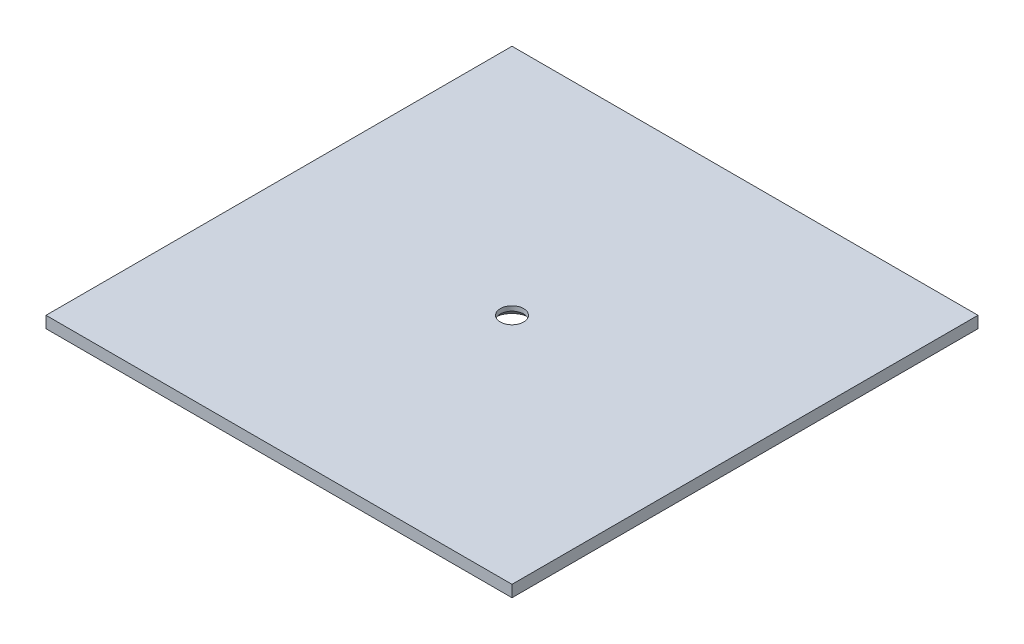
SolidWorks part; units mm, degrees
ref_plane "Спереди" through (0, 0, 0) normal (0, 0, 1) x (1, 0, 0)
ref_plane "Сверху" through (0, 0, 0) normal (0, 1, 0) x (1, 0, 0)
ref_plane "Справа" through (0, 0, 0) normal (1, 0, 0) x (0, 0, -1)
sketch "Эскиз1" plane through (0, 0, 0) normal (0, 1, 0) x (1, 0, 0)
  line L1 (-100, -100) -> (100, -100)
  line L2 (-100, -100) -> (-100, 100)
  line L3 (-100, 100) -> (100, 100)
  line L4 (100, -100) -> (100, 100)
  line L5 (-100, -100) -> (100, 100) construction
  line L6 (-100, 100) -> (100, -100) construction
  circle A0 centre (0, 0) radius 5
  point P0 (0, 0)
  dimension "D2" = 10
  dimension "D1" = 200
extrude "Бобышка-Вытянуть1" add sketch "Эскиз1" along normal blind 5
chamfer "Фаска1" distance 3 angle 45 1 edges at (0, 0, 5)
